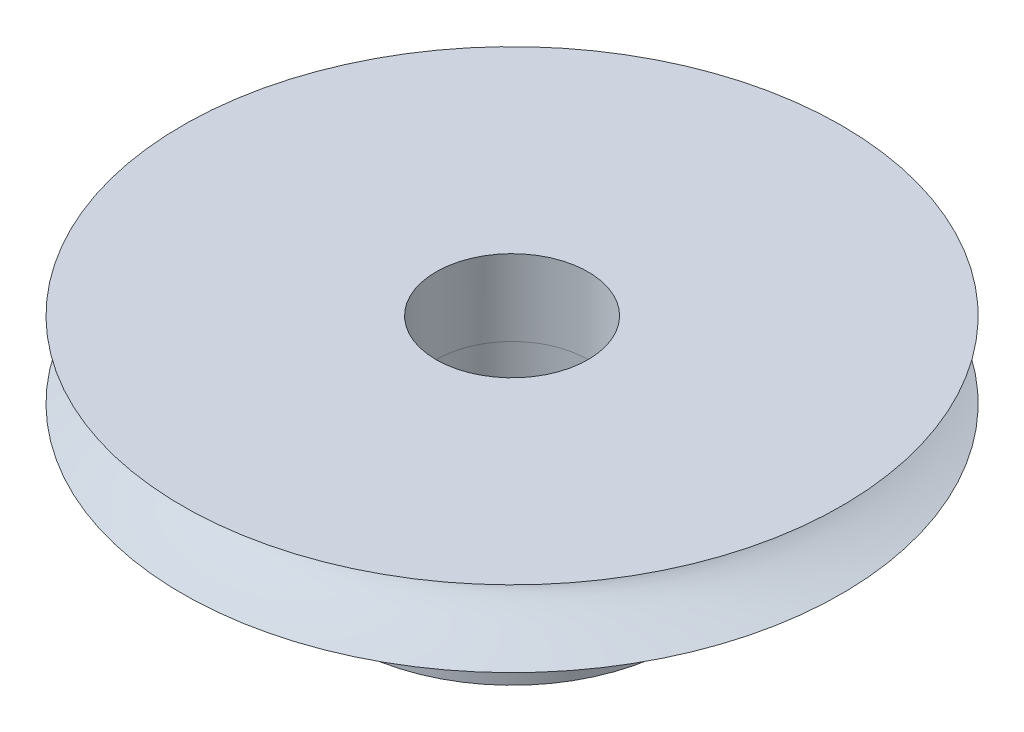
SolidWorks part; units mm, degrees
ref_plane "Front Plane" through (0, 0, 0) normal (0, 0, 1) x (1, 0, 0)
ref_plane "Top Plane" through (0, 0, 0) normal (0, 1, 0) x (1, 0, 0)
ref_plane "Right Plane" through (0, 0, 0) normal (1, 0, 0) x (0, 0, -1)
sketch "Sketch9" plane through (0, 0, 0) normal (0, 0, 1) x (1, 0, 0)
  line L0 (-4.7031, 0.0646) -> (0.1321, -1.2942) construction
  line L1 (-4.7031, -2.9354) -> (8.2969, -2.9354)
  line L3 (-4.7031, 0.0646) -> (8.2969, 0.0646)
  line L4 (8.2969, -2.9354) -> (8.2969, 0.0646)
  line L5 (0.1321, -1.2942) -> (-4.7031, -2.9354) construction
  spline S0 degree 2 poles (-4.7031, 0.0646) (0.1321, -1.2942) (-4.7031, -2.9354) knots 0 0 0 1 1 1
  point P5 (0, 0)
  dimension "D3" = 13
  dimension "D1" = 3
  dimension "D2" = 13
revolve "Revolve1" add sketch "Sketch9" angle 360 about L4
sketch "Sketch117" plane through (0, 0.0646, 0) normal (0, 1, 0) x (1, 0, 0)
  circle A0 centre (8.2969, 0) radius 3
extrude "Cut-Extrude4" cut sketch "Sketch117" against normal blind 3
sketch "Sketch122" plane through (0, -2.9354, 0) normal (0, -1, 0) x (-1, 0, 0)
  circle A0 centre (-8.2969, 0) radius 6.5398
extrude "Boss-Extrude1" add sketch "Sketch122" along normal blind 5
sketch "Sketch123" plane through (0, -2.9354, 0) normal (0, 1, 0) x (1, 0, 0)
  circle A0 centre (8.333, 0) radius 3.036
extrude "Cut-Extrude5" cut sketch "Sketch123" against normal blind 5
hole_wizard "M2x0.4 Tapped Hole1" positions "3DSketch1" profile "Sketch124" tap size "M2x0.4" standard "ANSI Metric" end condition through all
sketch3d "3DSketch1"
  circle A0 centre (8.2969, -2.9354, 0) radius 6.5398 construction
  circle A1 centre (8.2969, -7.9354, 0) radius 6.5398 construction
  point P0 (1.8154, -5.4316, -0.8709)
  point P5 (8.2969, -9.4751, 0)
  point P8 (8.2969, -14.4751, 0)
  dimension "D1" = 7
  dimension "D2" = 7.0027
sketch "Sketch124" plane through (1.8154, -5.4316, -0.8709) normal (0, 1, 0) x (-0.1332, 0, 0.9911)
  line L0 (0, 0) -> (0, 21.1551)
  line L1 (0, 21.1551) -> (0.8, 21.1551)
  line L2 (0.8, 21.1551) -> (0.8, 0)
  line L5 (0.8, 0) -> (0, 0)
  line L11 (0, -6.35) -> (0, 107.95) construction
  dimension "Thru Tap Drill Dia." = 1.6
  dimension "Thru Tap Drill Depth" = 21.1551
cosmetic thread "Hole Thread1" parameters "D2"=2
